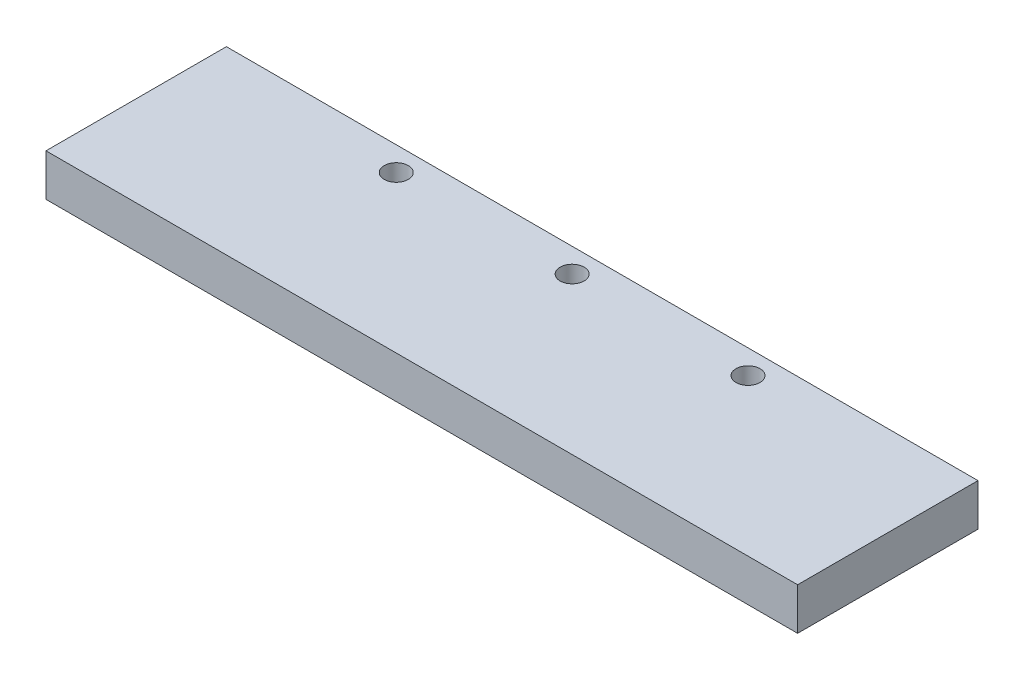
SolidWorks part; units mm, degrees
ref_plane "Front Plane" through (0, 0, 0) normal (0, 0, 1) x (1, 0, 0)
ref_plane "Top Plane" through (0, 0, 0) normal (0, 1, 0) x (1, 0, 0)
ref_plane "Right Plane" through (0, 0, 0) normal (1, 0, 0) x (0, 0, -1)
sketch "Sketch1" plane through (0, 0, 0) normal (0, 1, 0) x (1, 0, 0)
  line L1 (-102.5105, 65.1674) -> (22.4895, 65.1674)
  line L2 (-102.5105, 65.1674) -> (-102.5105, 35.1674)
  line L3 (-102.5105, 35.1674) -> (22.4895, 35.1674)
  line L4 (22.4895, 65.1674) -> (22.4895, 35.1674)
  dimension "D1" = 30
  dimension "D2" = 125
extrude "Boss-Extrude1" add sketch "Sketch1" along normal blind 7 contours L2 L3 L4 L1
sketch "Sketch2" plane through (0, 0, 0) normal (0, -1, 0) x (1, 0, 0)
  line L0 (-102.5105, -65.1674) -> (-102.5105, -35.1674) construction
  line L1 (-102.5105, -65.1674) -> (22.4895, -65.1674) construction
  circle A0 centre (-70.2605, -61.1674) radius 2
  circle A1 centre (-41.0105, -61.1674) radius 2
  circle A2 centre (-11.7605, -61.1674) radius 2
  dimension "D1" = 32.25
  dimension "D5" = 29.25
  dimension "D2" = 4
  dimension "D3" = 29.25
  dimension "D4" = 4
  dimension "D6" = 4
extrude "Cut-Extrude1" cut sketch "Sketch2" against normal blind 10
